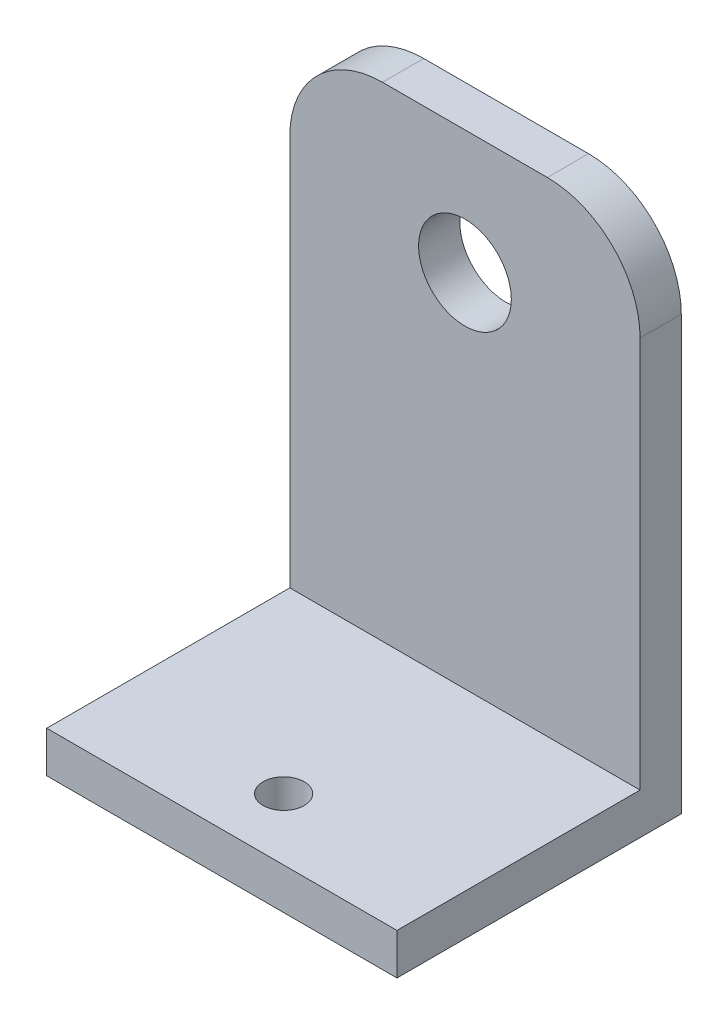
SolidWorks part; units mm, degrees
ref_plane "Front Plane" through (0, 0, 0) normal (0, 0, 1) x (1, 0, 0)
ref_plane "Top Plane" through (0, 0, 0) normal (0, 1, 0) x (1, 0, 0)
ref_plane "Right Plane" through (0, 0, 0) normal (1, 0, 0) x (0, 0, -1)
sketch "Sketch2" plane through (0, 0, 0) normal (0, 1, 0) x (1, 0, 0)
  line L1 (-17, -13.8) -> (17, -13.8)
  line L2 (-17, -13.8) -> (-17, 13.8)
  line L3 (-17, 13.8) -> (17, 13.8)
  line L4 (17, -13.8) -> (17, 13.8)
  line L5 (-17, -13.8) -> (17, 13.8) construction
  line L6 (-17, 13.8) -> (17, -13.8) construction
  circle A0 centre (0, -7.8) radius 2
  point P0 (0, 0)
  dimension "D3" = 4
  dimension "D4" = 6
  dimension "D1" = 34
  dimension "D2" = 27.6
extrude "Boss-Extrude1" add sketch "Sketch2" along normal blind 4
sketch "Sketch3" plane through (0, 4, 0) normal (0, 1, 0) x (1, 0, 0)
  line L0 (17, -13.8) -> (17, 13.8) construction
  line L1 (-17, 13.8) -> (17, 13.8)
  line L2 (-17, 13.8) -> (-17, 9.8)
  line L3 (-17, 9.8) -> (17, 9.8)
  line L4 (17, 13.8) -> (17, 9.8)
  dimension "D1" = 4
extrude "Boss-Extrude2" add sketch "Sketch3" along normal blind 47
fillet "Fillet1" radius 9 2 edges at (17, 51, -11.8) (-17, 51, -11.8)
sketch "Sketch4" plane through (0, 0, -9.8) normal (0, 0, 1) x (1, 0, 0)
  line L0 (-8, 51) -> (8, 51) construction
  circle A0 centre (0, 39) radius 4.5
  dimension "D1" = 12
  dimension "D2" = 9
extrude "Cut-Extrude1" cut sketch "Sketch4" against normal through all
